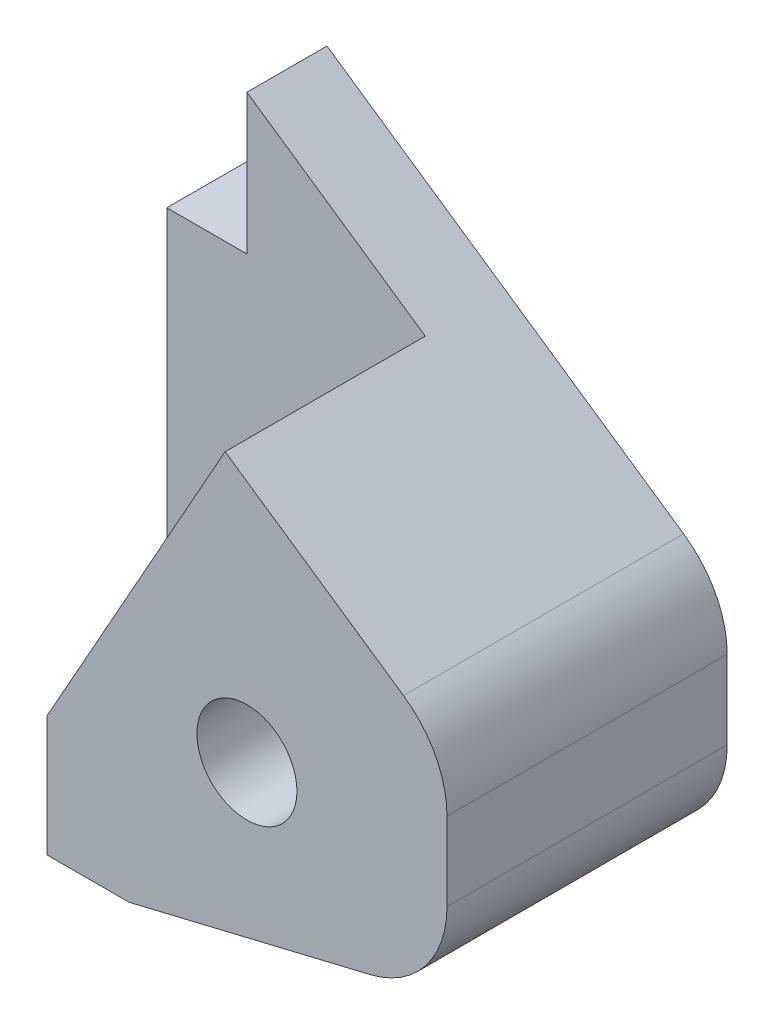
SolidWorks part; units mm, degrees
material "ﾊﾞﾙｻ"
ref_plane "正面" through (0, 0, 0) normal (0, 0, 1) x (1, 0, 0)
ref_plane "平面" through (0, 0, 0) normal (0, 1, 0) x (1, 0, 0)
ref_plane "右側面" through (0, 0, 0) normal (1, 0, 0) x (0, 0, -1)
sketch "ｽｹｯﾁ1" plane through (0, 0, 0) normal (0, 0, 1) x (1, 0, 0)
  line L0 (0, 0) -> (0, 15)
  line L1 (0, 15) -> (4, 15)
  line L2 (4, 15) -> (4, 22)
  line L3 (4, 22) -> (24, 22)
  line L4 (24, 22) -> (24, -6)
  line L5 (24, -6) -> (4, -6)
  line L6 (4, -6) -> (4, 0)
  line L7 (4, 0) -> (0, 0)
  line L8 (14, 22) -> (14, -6) construction
  line L9 (4, 22) -> (24, 8.3124)
  line L10 (8.1108, -6) -> (24, -2.1832)
  circle A0 centre (14, 3) radius 2.5
  dimension "D6" = 5
  dimension "D7" = 9
  dimension "D1" = 15
  dimension "D2" = 6
  dimension "D3" = 7
  dimension "D4" = 4
  dimension "D5" = 20
extrude "ﾎﾞｽ - 押し出し1" add sketch "ｽｹｯﾁ1" along normal blind 4 contours L5 L10 L4 L3 L2 L1 L0 L7 L6 A0 | L9 L8 A0 L10 L4
fillet "ﾌｨﾚｯﾄ1" radius 5 2 edges at (24, 8.3124, 2) (24, -2.1832, 2)
sketch "ｽｹｯﾁ2" plane through (0, 0, 4) normal (0, 0, 1) x (1, 0, 0)
  line L0 (4, -6) -> (4, 0) construction
  line L1 (8.1108, -6) -> (4, -6) construction
  line L2 (8.1108, -6) -> (20.1678, -3.1038) construction
  line L3 (24, 5.6755) -> (24, 1.7579) construction
  line L4 (4, 22) -> (21.8239, 9.8017) construction
  line L5 (4, -6) -> (4, 0)
  line L6 (8.1108, -6) -> (4, -6)
  line L7 (8.1108, -6) -> (20.1678, -3.1038)
  line L8 (24, 5.6755) -> (24, 1.7579)
  line L9 (4, 22) -> (21.8239, 9.8017)
  line L10 (4, 0) -> (12.9119, 15.9008)
  arc A0 (20.1678, -3.1038) -> (24, 1.7579) centre (19, 1.7579) ccw construction
  arc A1 (24, 5.6755) -> (21.8239, 9.8017) centre (19, 5.6755) ccw construction
  arc A2 (20.1678, -3.1038) -> (24, 1.7579) centre (19, 1.7579) ccw
  arc A3 (24, 5.6755) -> (21.8239, 9.8017) centre (19, 5.6755) ccw
  circle A4 centre (14, 3) radius 2.5 construction
  circle A5 centre (14, 3) radius 2.5
  circle M1 centre (14, 3) radius 2.5
  line M2 (24, 1.7579) -> (24, 5.6755)
  arc M3 (24, 5.6755) -> (21.8239, 9.8017) centre (19, 5.6755) ccw
  line M4 (21.8239, 9.8017) -> (4, 22)
  line M9 (4, 0) -> (4, -6)
  line M10 (4, -6) -> (8.1108, -6)
  line M11 (8.1108, -6) -> (20.1678, -3.1038)
  arc M12 (20.1678, -3.1038) -> (24, 1.7579) centre (19, 1.7579) ccw
extrude "ﾎﾞｽ - 押し出し2" add sketch "ｽｹｯﾁ2" along normal blind 10 contours L10 M9 M10 M11 M12 M2 M3 M4 M1
